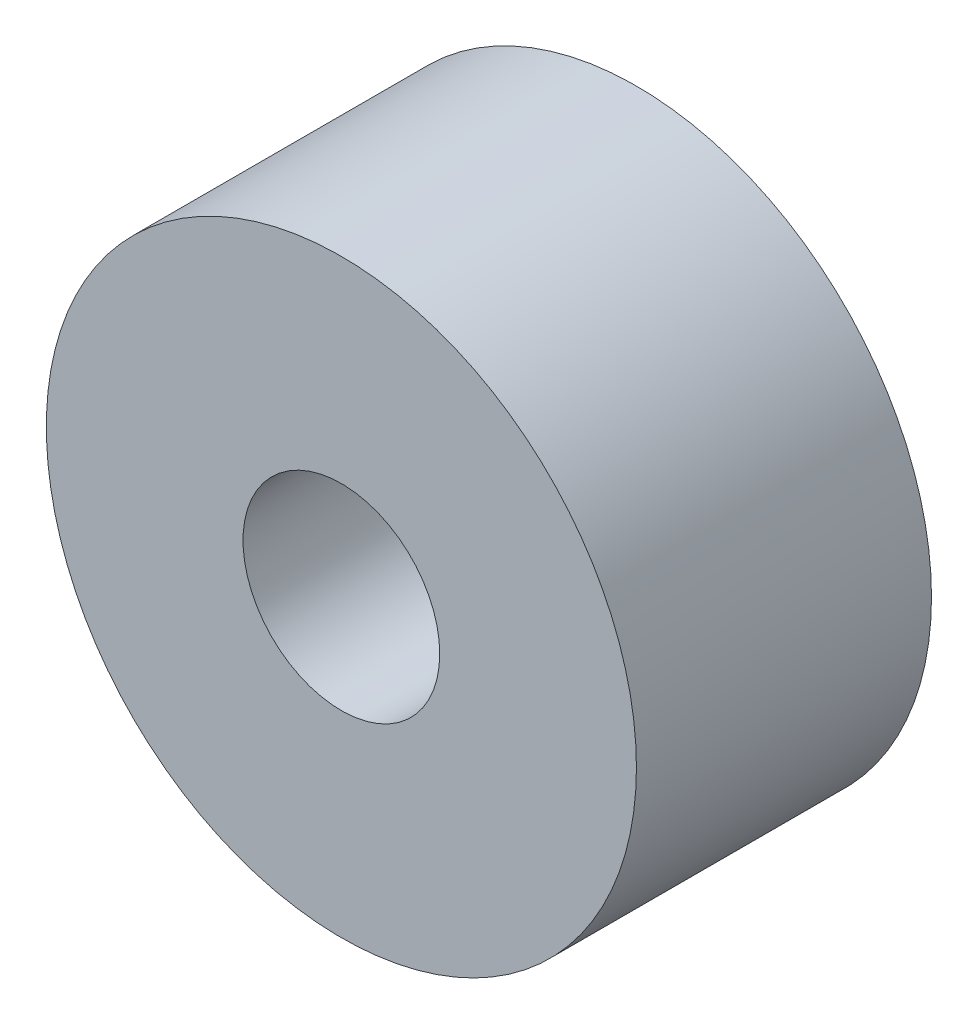
SolidWorks part; units mm, degrees
ref_plane "Plan de face" through (0, 0, 0) normal (0, 0, 1) x (1, 0, 0)
ref_plane "Plan de dessus" through (0, 0, 0) normal (0, 1, 0) x (1, 0, 0)
ref_plane "Plan de droite" through (0, 0, 0) normal (1, 0, 0) x (0, 0, -1)
sketch "Esquisse1" plane through (0, 0, 0) normal (1, 0, 0) x (0, 0, -1)
  line L0 (0, 0) -> (0, 2.1481) construction
  line L1 (0, 0) -> (3.9506, 0) construction
  line L2 (-1.5, 3) -> (1.5, 3)
  line L3 (-1.5, 3) -> (-1.5, 1)
  line L4 (-1.5, 1) -> (1.5, 1)
  line L5 (1.5, 3) -> (1.5, 1)
  dimension "D1" = 2
  dimension "D2" = 6
  dimension "D3" = 3
revolve "Révolution1" add sketch "Esquisse1" angle 360 about L1
